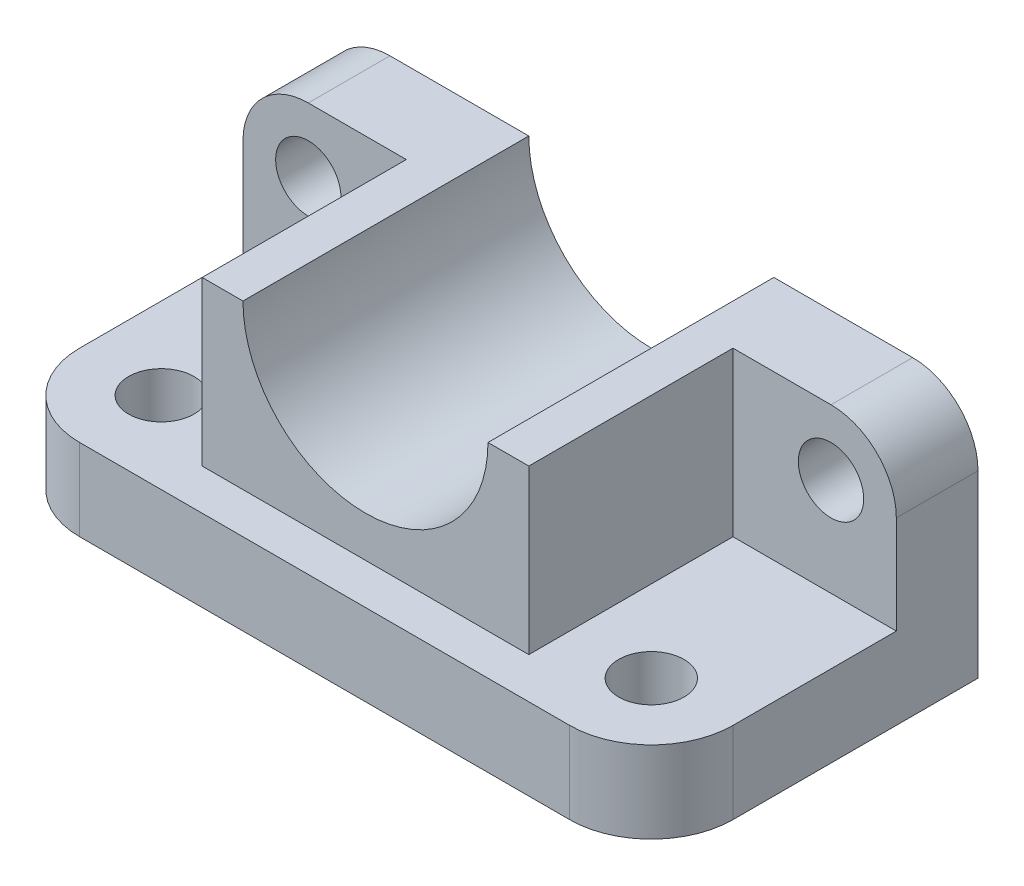
SolidWorks part; units mm, degrees
material "회주철"
ref_plane "정면" through (0, 0, 0) normal (0, 0, 1) x (1, 0, 0)
ref_plane "윗면" through (0, 0, 0) normal (0, 1, 0) x (1, 0, 0)
ref_plane "우측면" through (0, 0, 0) normal (1, 0, 0) x (0, 0, -1)
sketch "스케치1" plane through (0, 0, 0) normal (0, 1, 0) x (1, 0, 0)
  line L1 (-30, -20) -> (30, -20)
  line L2 (-40, -10) -> (-40, 20)
  line L3 (-40, 20) -> (40, 20)
  line L4 (40, -10) -> (40, 20)
  line L5 (-40, -20) -> (40, 20) construction
  line L6 (-40, 20) -> (40, -20) construction
  arc A0 (40, -10) -> (30, -20) centre (30, -10) cw
  arc A1 (-30, -20) -> (-40, -10) centre (-30, -10) cw
  circle A2 centre (-30, -10) radius 4
  circle A3 centre (30, -10) radius 4
  point P0 (0, 0)
  dimension "D3" = 10
  dimension "D4" = 8
  dimension "D1" = 40
  dimension "D2" = 80
extrude "보스-돌출1" add sketch "스케치1" along normal blind 30
sketch "스케치2" plane through (0, 30, 0) normal (0, 1, 0) x (1, 0, 0)
  line L0 (40, -10) -> (40, 20) construction
  line L1 (-30, -20) -> (30, -20) construction
  line L2 (-40, 20) -> (-40, -10) construction
  line L3 (40, -10) -> (40, 10)
  line L4 (-30, -20) -> (30, -20)
  line L5 (-40, 10) -> (-40, -10)
  line L7 (-20, 10) -> (-20, -15)
  line L8 (20, -15) -> (20, 10)
  line L9 (40, 10) -> (20, 10)
  line L11 (-20, 20) -> (-20, -10) construction
  line L12 (20, -15) -> (-20, -15)
  line L13 (-20, 10) -> (-40, 10)
  line L14 (20, -10) -> (20, 20) construction
  line L15 (-40, 20) -> (-40, -10) construction
  line L16 (40, -10) -> (40, 20) construction
  line L17 (40, 20) -> (-40, 20) construction
  arc A0 (30, -20) -> (40, -10) centre (30, -10) ccw construction
  arc A1 (-40, -10) -> (-30, -20) centre (-30, -10) ccw construction
  arc A2 (30, -20) -> (40, -10) centre (30, -10) ccw
  arc A3 (-40, -10) -> (-30, -20) centre (-30, -10) ccw
  dimension "D1" = 35
extrude "컷-돌출1" cut sketch "스케치2" against normal blind 20
fillet "필렛1" radius 8 2 edges at (40, 30, -15) (-40, 30, -15)
sketch "스케치3" plane through (0, 0, 20) normal (0, 0, 1) x (1, 0, 0)
  line L0 (20, 30) -> (-20, 30) construction
  line L1 (15, 30) -> (-15, 30)
  arc A0 (-15, 30) -> (15, 30) centre (0, 30) ccw
  circle A1 centre (-32, 22) radius 4
  circle A2 centre (32, 22) radius 4
  dimension "D1" = 15
  dimension "D2" = 8
extrude "컷-돌출2" cut sketch "스케치3" against normal through all
